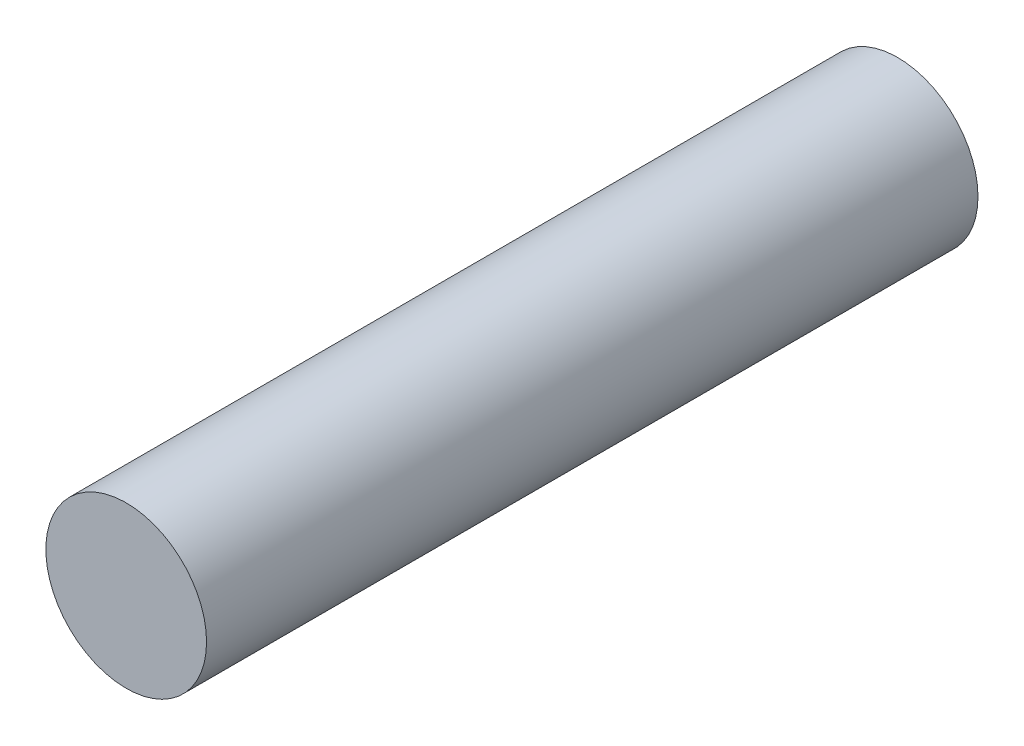
SolidWorks part; units mm, degrees
ref_plane "前视基准面" through (0, 0, 0) normal (0, 0, 1) x (1, 0, 0)
ref_plane "上视基准面" through (0, 0, 0) normal (0, 1, 0) x (1, 0, 0)
ref_plane "右视基准面" through (0, 0, 0) normal (1, 0, 0) x (0, 0, -1)
sketch "草图1" plane through (0, 0, 0) normal (0, 0, 1) x (1, 0, 0)
  circle A0 centre (0, 0) radius 1.25
  dimension "D1" = 2.5
extrude "凸台-拉伸1" add sketch "草图1" along normal blind 12
